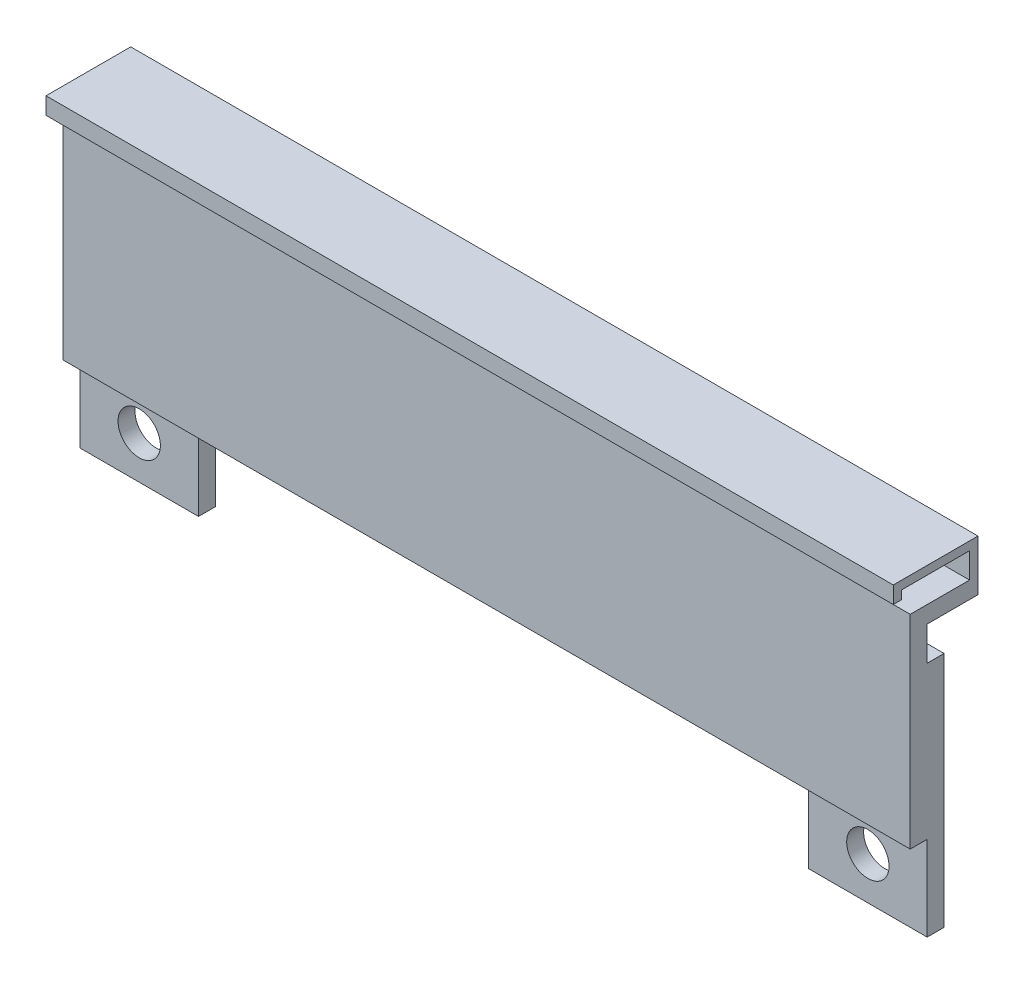
SolidWorks part; units mm, degrees
material "ABS"
ref_plane "Plan de face" through (0, 0, 0) normal (0, 0, 1) x (1, 0, 0)
ref_plane "Plan de dessus" through (0, 0, 0) normal (0, 1, 0) x (1, 0, 0)
ref_plane "Plan de droite" through (0, 0, 0) normal (1, 0, 0) x (0, 0, -1)
sketch "Esquisse1" plane through (0, 0, 0) normal (0, 0, 1) x (1, 0, 0)
  line L0 (-100, 5) -> (0, 5) construction
  line L1 (0, 0) -> (-100, 0)
  line L2 (0, 0) -> (0, 12)
  line L3 (0, 12) -> (-100, 12)
  line L4 (-100, 0) -> (-100, 12)
  line L5 (-100, 0) -> (0, 0)
  line L6 (-100, 0) -> (-100, 10)
  line L7 (-100, 10) -> (0, 10)
  line L8 (0, 0) -> (0, 10)
  circle A0 centre (-93, 5) radius 2.5
  circle A1 centre (-7, 5) radius 2.5
  dimension "D6" = 5
  dimension "D8" = 5
  dimension "D1" = 100
  dimension "D2" = 12
  dimension "D3" = 10
  dimension "D4" = 5
  dimension "D5" = 7
  dimension "D7" = 7
extrude "Boss.-Extru.1" add sketch "Esquisse1" along normal blind 2 contours L4 L7 L2 L3 | L6 L0 A0 A1 L8 L7 | L0 L4 L1 L2 A1 A0
sketch "Esquisse2" plane through (0, 0, 0) normal (0, 0, -1) x (-1, 0, 0)
  line L0 (100, 0) -> (100, 12) construction
  line L1 (0, 12) -> (100, 12)
  line L2 (0, 12) -> (0, 10)
  line L3 (0, 10) -> (100, 10)
  line L4 (100, 12) -> (100, 10)
  dimension "D1" = 2
extrude "Boss.-Extru.2" add sketch "Esquisse2" along normal blind 2
sketch "Esquisse3" plane through (0, 12, 0) normal (0, 1, 0) x (1, 0, 0)
  line L1 (-100, 2) -> (0, 2)
  line L2 (-100, 2) -> (-100, -2)
  line L3 (-100, -2) -> (0, -2)
  line L4 (0, 2) -> (0, -2)
extrude "Boss.-Extru.3" add sketch "Esquisse3" along normal blind 22
sketch "Esquisse4" plane through (0, 34, 0) normal (0, 1, 0) x (1, 0, 0)
  line L1 (-100, -2) -> (0, -2)
  line L2 (-100, -2) -> (-100, 0)
  line L3 (-100, 0) -> (0, 0)
  line L4 (0, -2) -> (0, 0)
extrude "Enlèv. mat.-Extru.1" cut sketch "Esquisse4" against normal blind 6
sketch "Esquisse5" plane through (0, 0, -2) normal (0, 0, -1) x (-1, 0, 0)
  line L0 (100, 10) -> (100, 34) construction
  line L1 (0, 34) -> (100, 34)
  line L2 (0, 34) -> (0, 32)
  line L3 (0, 32) -> (100, 32)
  line L4 (100, 34) -> (100, 32)
  dimension "D1" = 2
extrude "Boss.-Extru.4" add sketch "Esquisse5" along normal blind 6
sketch "Esquisse6" plane through (0, 0, -8) normal (0, 0, -1) x (-1, 0, 0)
  line L1 (0, 32) -> (100, 32)
  line L2 (0, 32) -> (0, 38)
  line L3 (0, 38) -> (100, 38)
  line L4 (100, 32) -> (100, 38)
  dimension "D1" = 100
  dimension "D2" = 6
extrude "Boss.-Extru.5" add sketch "Esquisse6" against normal blind 1
sketch "Esquisse9" plane through (0, 0, -7) normal (0, 0, 1) x (1, 0, 0)
  line L0 (0, 38) -> (0, 34) construction
  line L1 (-100, 38) -> (0, 38)
  line L2 (-100, 38) -> (-100, 37)
  line L3 (-100, 37) -> (0, 37)
  line L4 (0, 38) -> (0, 37)
  dimension "D1" = 1
extrude "Boss.-Extru.8" add sketch "Esquisse9" along normal blind 9
sketch "Esquisse10" plane through (0, 37, 0) normal (0, -1, 0) x (1, 0, 0)
  line L0 (0, 2) -> (0, -7) construction
  line L1 (-100, 2) -> (0, 2)
  line L2 (-100, 2) -> (-100, 1)
  line L3 (-100, 1) -> (0, 1)
  line L4 (0, 2) -> (0, 1)
  dimension "D1" = 1
extrude "Boss.-Extru.9" add sketch "Esquisse10" along normal blind 1
sketch "Esquisse11" plane through (0, 0, -2) normal (0, 0, -1) x (-1, 0, 0)
  line L0 (100, 10) -> (100, 32) construction
  line L1 (100, 28) -> (0, 28)
  line L2 (100, 28) -> (100, 0)
  line L3 (100, 0) -> (0, 0)
  line L4 (0, 28) -> (0, 0)
  circle A0 centre (93, 5) radius 2.5
  circle A1 centre (7, 5) radius 2.5
  dimension "D2" = 5
  dimension "D3" = 5
  dimension "D1" = 28
extrude "Boss.-Extru.10" add sketch "Esquisse11" along normal blind 2
sketch "Esquisse12" plane through (0, 0, 2) normal (0, 0, 1) x (1, 0, 0)
  line L1 (-100, 28) -> (0, 28)
  line L2 (-100, 28) -> (-100, 0)
  line L3 (-100, 0) -> (0, 0)
  line L4 (0, 28) -> (0, 0)
extrude "Enlèv. mat.-Extru.2" cut sketch "Esquisse12" against normal blind 2
sketch "Esquisse13" plane through (0, 0, -2) normal (0, 0, 1) x (1, 0, 0)
  line L0 (0, 0) -> (-100, 0) construction
  line L1 (-86, 0) -> (-14, 0)
  line L2 (-86, 0) -> (-86, 10)
  line L3 (-86, 10) -> (-14, 10)
  line L4 (-14, 0) -> (-14, 10)
  line L5 (0, 10) -> (-100, 10) construction
  line L6 (-100, 0) -> (-100, 10) construction
  line L7 (0, 10) -> (0, 0) construction
  dimension "D1" = 14
  dimension "D2" = 14
extrude "Enlèv. mat.-Extru.3" cut sketch "Esquisse13" against normal blind 2
